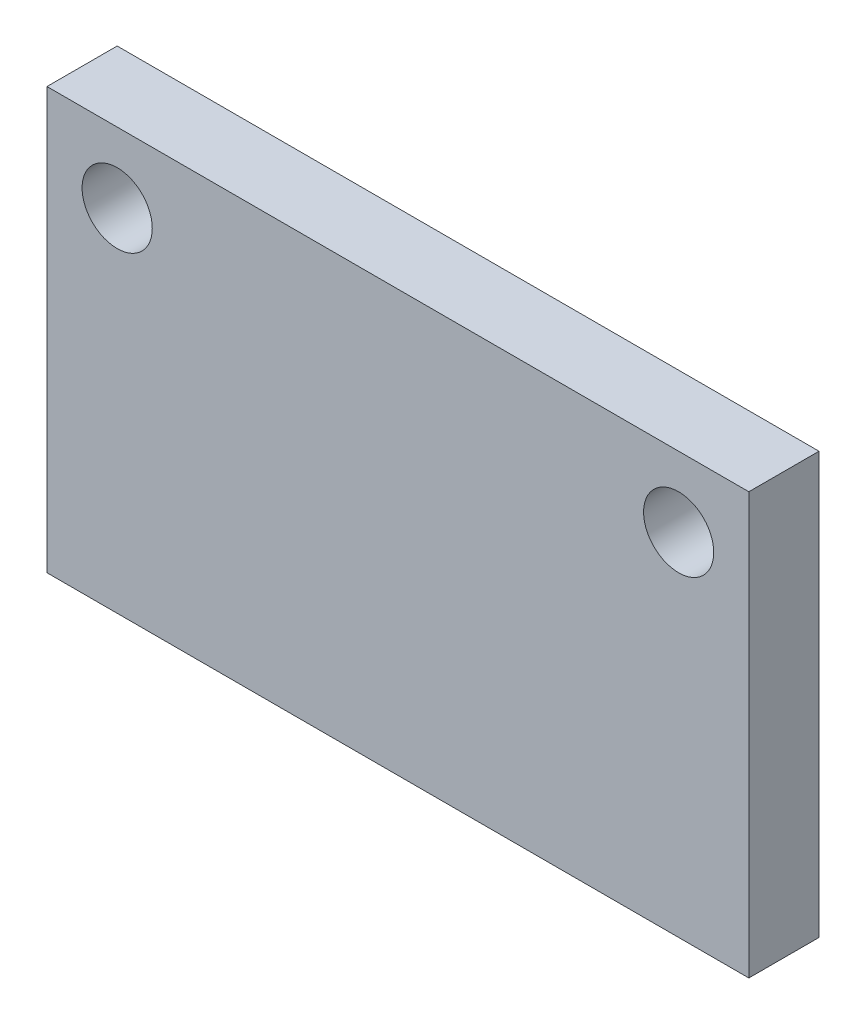
SolidWorks part; units mm, degrees
ref_plane "Front Plane" through (0, 0, 0) normal (0, 0, 1) x (1, 0, 0)
ref_plane "Top Plane" through (0, 0, 0) normal (0, 1, 0) x (1, 0, 0)
ref_plane "Right Plane" through (0, 0, 0) normal (1, 0, 0) x (0, 0, -1)
sketch "Sketch1" plane through (0, 0, 0) normal (0, 0, 1) x (1, 0, 0)
  line L0 (0, 7.62) -> (0, -7.62) construction
  line L1 (-12.7, -7.62) -> (12.7, -7.62)
  line L2 (-12.7, -7.62) -> (-12.7, 7.62)
  line L3 (-12.7, 7.62) -> (12.7, 7.62)
  line L4 (12.7, -7.62) -> (12.7, 7.62)
  line L5 (-12.7, -7.62) -> (12.7, 7.62) construction
  line L6 (-12.7, 7.62) -> (12.7, -7.62) construction
  circle A0 centre (-10.16, 5.08) radius 1.27
  circle A1 centre (10.16, 5.08) radius 1.27
  point P0 (0, 0)
  dimension "D3" = 2.54
  dimension "D1" = 25.4
  dimension "D2" = 15.24
  dimension "D4" = 2.54
extrude "Boss-Extrude1" add sketch "Sketch1" along normal blind 2.54
